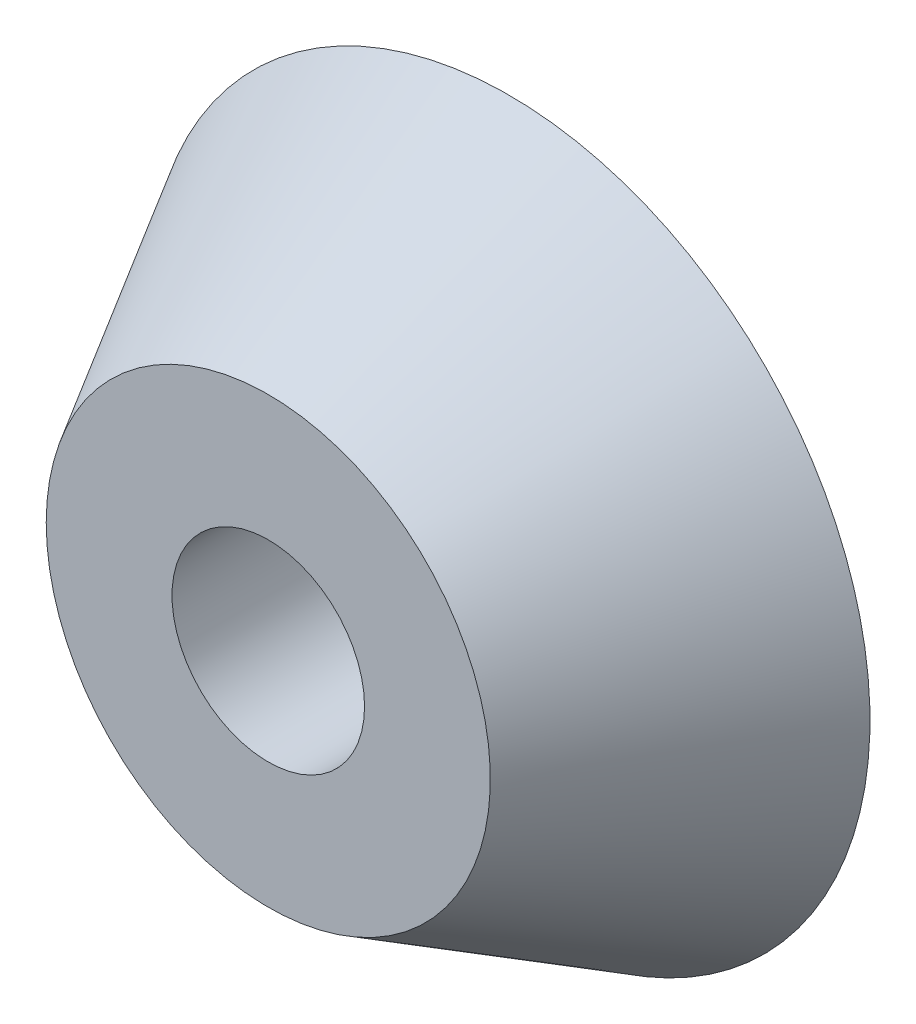
SolidWorks part; units mm, degrees
material "Brass"
ref_plane "Front Plane" through (0, 0, 0) normal (0, 0, 1) x (1, 0, 0)
ref_plane "Top Plane" through (0, 0, 0) normal (0, 1, 0) x (1, 0, 0)
ref_plane "Right Plane" through (0, 0, 0) normal (1, 0, 0) x (0, 0, -1)
sketch "Sketch2" plane through (0, 0, 0) normal (0, 1, 0) x (1, 0, 0)
  line L0 (0, 0) -> (23.0662, 0)
  line L1 (23.0662, 0) -> (37.5, 25)
  line L2 (37.5, 25) -> (0, 25)
  line L3 (0, 25) -> (0, 0)
  dimension "D1" = 37.5
  dimension "D2" = 60
  dimension "D3" = 25
revolve "Revolve1" add sketch "Sketch2" angle 360 about L3
sketch "Sketch3" plane through (0, 0, 0) normal (0, 0, 1) x (1, 0, 0)
  circle A0 centre (0, 0) radius 10
  dimension "D1" = 20
extrude "Cut-Extrude1" cut sketch "Sketch3" against normal through all
